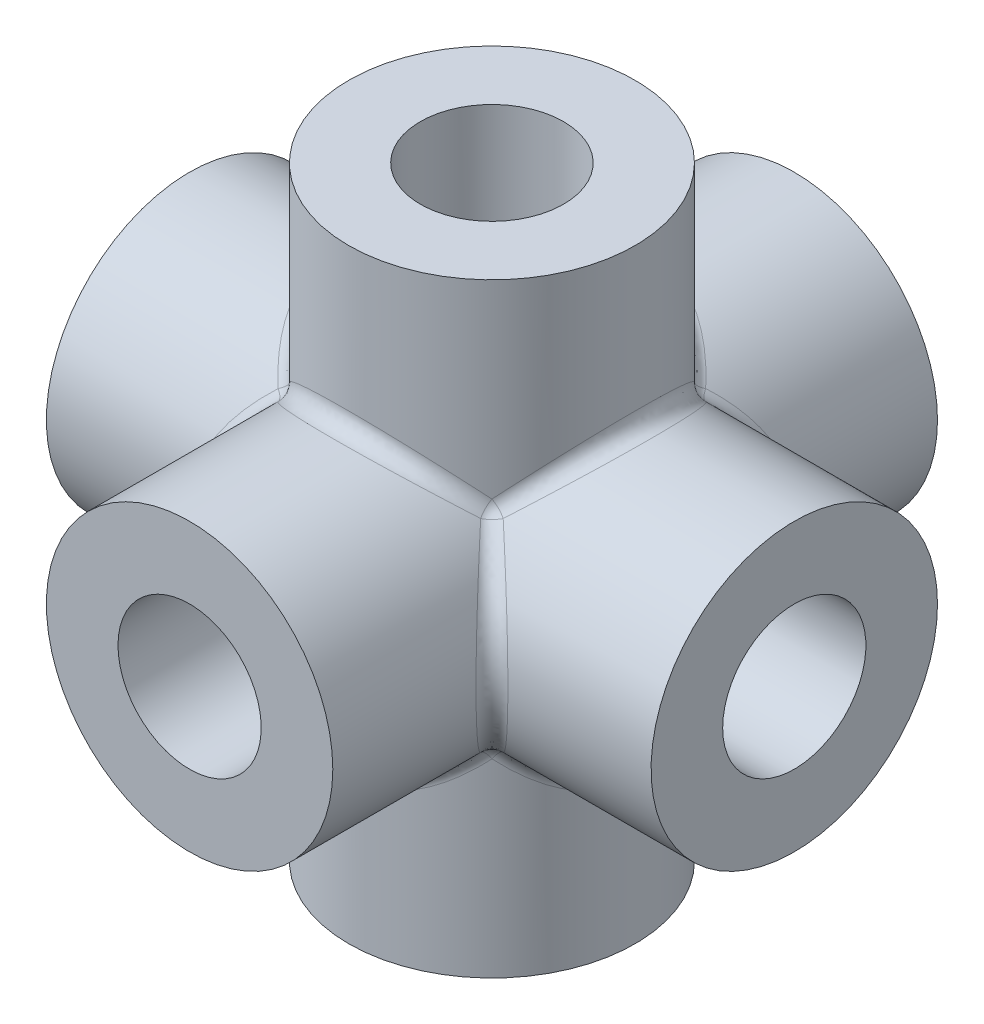
SolidWorks part; units mm, degrees
ref_plane "Front Plane" through (0, 0, 0) normal (0, 0, 1) x (1, 0, 0)
ref_plane "Top Plane" through (0, 0, 0) normal (0, 1, 0) x (1, 0, 0)
ref_plane "Right Plane" through (0, 0, 0) normal (1, 0, 0) x (0, 0, -1)
sketch "Sketch1" plane through (0, 0, 0) normal (0, 0, 1) x (1, 0, 0)
  circle A0 centre (0, 0) radius 4.5
  dimension "D1" = 9
extrude "Boss-Extrude2" add sketch "Sketch1" along normal mid plane 19
sketch "Sketch4" plane through (0, 0, 0) normal (0, 1, 0) x (1, 0, 0)
  circle A0 centre (0, 0) radius 4.5
extrude "Boss-Extrude3" add sketch "Sketch4" along normal mid plane 19
sketch "Sketch5" plane through (0, 0, 0) normal (1, 0, 0) x (0, 0, -1)
  circle A0 centre (0, 0) radius 4.5
extrude "Boss-Extrude4" add sketch "Sketch5" along normal mid plane 19
fillet "Fillet1" radius 0.5 12 edges at (0, 4.5, 4.5) (0, 4.5, -4.5) (4.5, 4.5, 0) (-4.5, 4.5, 0) (0, -4.5, -4.5) (0, -4.5, 4.5) (-4.5, -4.5, 0) (-4.5, 0, 4.5) (-4.5, 0, -4.5) (4.5, 0, 4.5) (4.5, -4.5, 0) (4.5, 0, -4.5)
sketch "Sketch6" plane through (0, 0, -9.5) normal (0, 0, -1) x (-1, 0, 0)
  circle A0 centre (0, 0) radius 2.25
extrude "Cut-Extrude1" cut sketch "Sketch6" against normal blind 19
sketch "Sketch7" plane through (-9.5, 0, 0) normal (-1, 0, 0) x (0, 0, 1)
  circle A0 centre (0, 0) radius 2.25
extrude "Cut-Extrude2" cut sketch "Sketch7" against normal blind 19
sketch "Sketch8" plane through (0, -9.5, 0) normal (0, -1, 0) x (1, 0, 0)
  circle A0 centre (0, 0) radius 2.25
extrude "Cut-Extrude3" cut sketch "Sketch8" against normal blind 19
